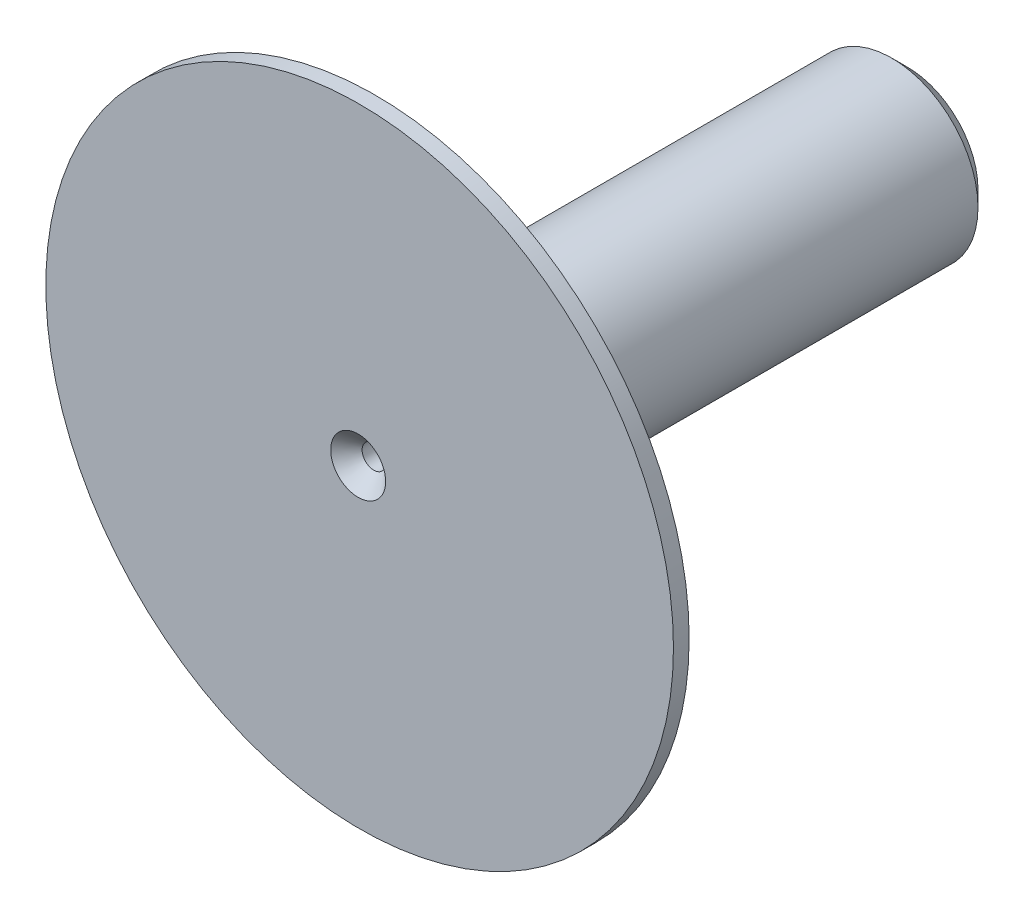
SolidWorks part; units mm, degrees
ref_plane "Front Plane" through (0, 0, 0) normal (0, 0, 1) x (1, 0, 0)
ref_plane "Top Plane" through (0, 0, 0) normal (0, 1, 0) x (1, 0, 0)
ref_plane "Right Plane" through (0, 0, 0) normal (1, 0, 0) x (0, 0, -1)
sketch "Sketch1" plane through (0, 0, 0) normal (0, 0, 1) x (1, 0, 0)
  circle A0 centre (0, 0) radius 0.15
  circle A1 centre (0, 0) radius 1.1
  dimension "D1" = 2.2
  dimension "D2" = 0.3
extrude "Boss-Extrude1" add sketch "Sketch1" along normal blind 7
sketch "Sketch2" plane through (0, 0, 7) normal (0, 0, 1) x (1, 0, 0)
  circle A0 centre (0, 0) radius 1.1
  circle A1 centre (0.0187, 0) radius 4
  circle A2 centre (0, 0) radius 1.1 construction
  dimension "D1" = 8
extrude "Boss-Extrude2" add sketch "Sketch2" against normal blind 0.2
chamfer "Chamfer1" distance 0.2 angle 45 3 edges at (1.1, 0, 0) (0.15, 0, 0) (0.15, 0, 7)
